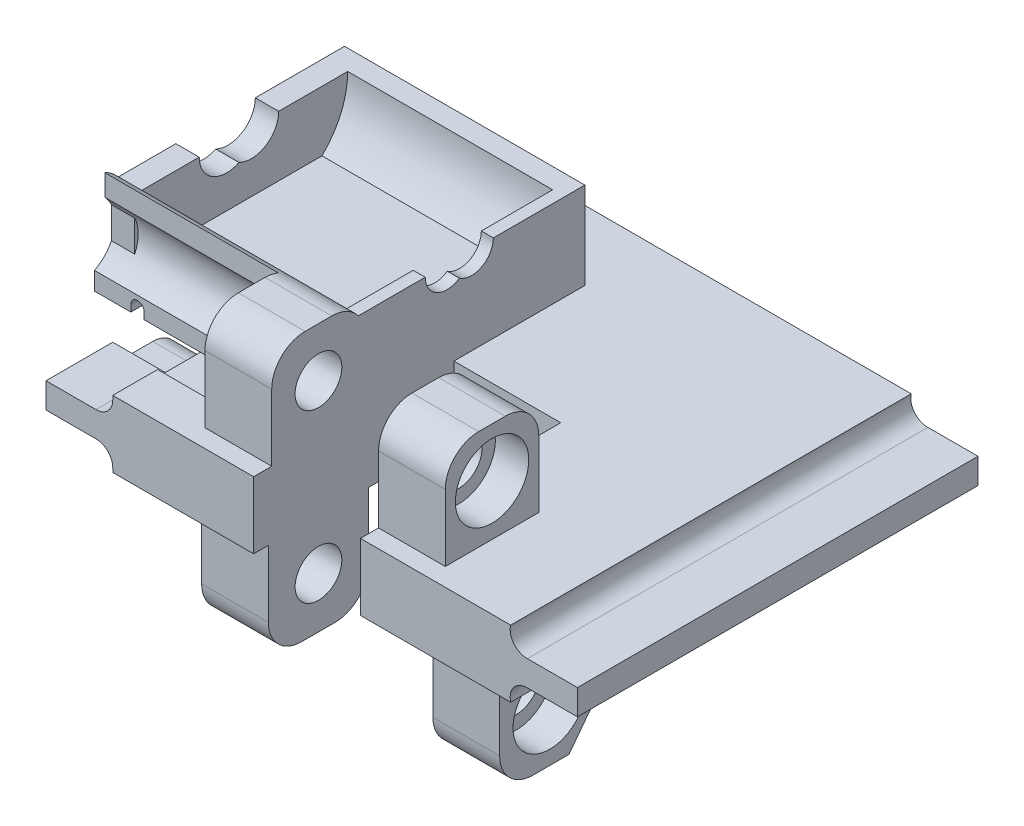
SolidWorks part; units mm, degrees
material "ABS"
ref_plane "정면" through (0, 0, 0) normal (0, 0, 1) x (1, 0, 0)
ref_plane "윗면" through (0, 0, 0) normal (0, 1, 0) x (1, 0, 0)
ref_plane "우측면" through (0, 0, 0) normal (1, 0, 0) x (0, 0, -1)
sketch "스케치1" plane through (0, 0, 0) normal (0, 0, 1) x (1, 0, 0)
  line L0 (0, 0) -> (0, 10)
  line L1 (29.8, 10) -> (-29.8, 10)
  line L2 (-32.3, 6.9) -> (-39.8, 6.9)
  line L3 (-39.8, 6.9) -> (-39.8, 3.1)
  line L4 (-39.8, 3.1) -> (-32.3, 3.1)
  line L5 (-29.8, 0) -> (29.8, 0)
  line L6 (39.8, 3.1) -> (32.3, 3.1)
  line L7 (39.8, 6.9) -> (39.8, 3.1)
  line L8 (32.3, 6.9) -> (39.8, 6.9)
  line L9 (-29.8, 10) -> (-29.8, 9.4)
  line L10 (-29.8, 0.6) -> (-29.8, 0)
  arc A2 (32.3, 3.1) -> (29.8, 0) centre (32.2267, 0.6011) ccw
  arc A3 (29.8, 10) -> (32.3, 6.9) centre (32.2267, 9.3989) ccw
  arc A5 (-32.3, 3.1) -> (-29.8, 0.6) centre (-32.3, 0.6) cw
  arc A6 (-29.8, 9.4) -> (-32.3, 6.9) centre (-32.3, 9.4) cw
  point P13 (0, 5)
  point P14 (-39.8, 5)
  dimension "D5" = 2.5
  dimension "D6" = 2.5
  dimension "D1" = 39.8
  dimension "D2" = 29.8
  dimension "D3" = 10
  dimension "D4" = 29.8
  dimension "D7" = 3.8
extrude "보스-돌출1" add sketch "스케치1" along normal blind 60
sketch "스케치2" plane through (-39.8, 0, 0) normal (-1, 0, 0) x (0, 0, 1)
  line L1 (44, 4) -> (50, 4)
  line L2 (50, 4) -> (50, 8)
  line L3 (16, 4) -> (10, 4)
  line L4 (50, 8) -> (10, 8)
  line L5 (30, 8) -> (30, 0)
  line L6 (20, 0) -> (40, 0)
  line L7 (60, 6.9) -> (60, 3.1) construction
  line L8 (10, 4) -> (10, 8)
  line L9 (60, 0) -> (0, 0) construction
  arc A0 (40, 0) -> (44, 4) centre (44, 0) cw
  arc A1 (20, 0) -> (16, 4) centre (16, 0) ccw
  line M12 (0, 3.1) -> (60, 3.1)
  line M14 (60, 6.9) -> (0, 6.9)
  dimension "D4" = 4
  dimension "D1" = 4
  dimension "D2" = 4
  dimension "D3" = 10
  dimension "D5" = 20
  dimension "D6" = 10
extrude "컷-돌출1" cut sketch "스케치2" against normal blind 17.3 contours A1 L5 L8 L3 M12 M14 | L6 A0 L5 M12 | A0 L1 L2 L5 M12 M14
sketch "Sketch1" plane through (0, 10, 0) normal (0, 1, 0) x (1, 0, 0)
  line L0 (29.8, -60) -> (-29.8, -60) construction
  line L1 (7.3, -60) -> (-8.7, -60)
  line L2 (7.3, -60) -> (7.3, -30)
  line L3 (7.3, -30) -> (-8.7, -30)
  line L4 (-8.7, -60) -> (-8.7, -30)
  line L5 (29.8, -60) -> (29.8, 0) construction
  dimension "D1" = 22.5
  dimension "D2" = 30
  dimension "D3" = 16
extrude "Cut-Extrude1" cut sketch "Sketch1" against normal blind 10
sketch "Sketch2" plane through (7.3, 0, 0) normal (-1, 0, 0) x (0, 0, 1)
  line L0 (60, 10) -> (30, 10) construction
  line L6 (57.29, 10) -> (43.29, 10)
  line L7 (57.29, 10) -> (57.29, 20)
  line L8 (52.29, 25) -> (48.29, 25)
  line L9 (43.29, 10) -> (43.29, 20)
  circle A0 centre (50.29, 17.61) radius 3.5
  arc A3 (48.29, 25) -> (43.29, 20) centre (48.29, 20) ccw
  arc A4 (57.29, 20) -> (52.29, 25) centre (52.29, 20) ccw
  point P1 (50.29, 25)
  point P11 (43.29, 25)
  point P15 (57.29, 25)
  dimension "D1" = 7
  dimension "D2" = 14
  dimension "D6" = 5
  dimension "D3" = 7.61
  dimension "D4" = 9.71
  dimension "D5" = 15
extrude "Boss-Extrude1" add sketch "Sketch2" against normal blind 10
sketch "Sketch4" plane through (17.3, 0, 0) normal (1, 0, 0) x (0, 0, -1)
  circle A0 centre (-50.29, 17.61) radius 5.5
  dimension "D1" = 11
extrude "Cut-Extrude4" cut sketch "Sketch4" against normal blind 5
ref_plane "Plane1" through (-0.7, 0, 0) normal (-1, 0, 0) x (0, 0, 1)
mirror "Mirror1" about plane through (-0.7, 0, 0) normal (-1, 0, 0) of "Cut-Extrude4", "Boss-Extrude1"
sketch "Sketch5" plane through (-8.7, 0, 0) normal (1, 0, 0) x (0, 0, -1)
  line L0 (-30, 0) -> (-60, 0) construction
  line L1 (-60, 0) -> (-60, 10) construction
  line L3 (-57.79, 0) -> (-42.79, 0)
  line L4 (-57.79, 0) -> (-57.79, -10)
  line L5 (-52.79, -15) -> (-47.79, -15)
  line L6 (-42.79, 0) -> (-42.79, -10)
  circle A0 centre (-50.29, -7.39) radius 3.5
  arc A1 (-47.79, -15) -> (-42.79, -10) centre (-47.79, -10) ccw
  arc A2 (-57.79, -10) -> (-52.79, -15) centre (-52.79, -10) ccw
  point P11 (-50.29, -15)
  point P14 (-42.79, -15)
  point P17 (-57.79, -15)
  dimension "D1" = 7
  dimension "D6" = 5
  dimension "D2" = 7.39
  dimension "D3" = 9.71
  dimension "D4" = 15
  dimension "D5" = 15
extrude "Boss-Extrude2" add sketch "Sketch5" against normal blind 10
sketch "Sketch6" plane through (-18.7, 0, 0) normal (-1, 0, 0) x (0, 0, 1)
  circle A0 centre (50.29, -7.39) radius 5.5
  dimension "D1" = 11
extrude "Cut-Extrude5" cut sketch "Sketch6" against normal blind 5
ref_plane "Plane2" through (3.62, 0, 0) normal (1, 0, 0) x (0, 0, -1)
mirror "Mirror2" about plane through (3.62, 0, 0) normal (1, 0, 0) of "Cut-Extrude5", "Boss-Extrude2"
sketch "Sketch7" plane through (-8.7, 0, 0) normal (1, 0, 0) x (0, 0, -1)
  line L0 (-30, 0) -> (-30, 10) construction
  line L1 (-30, 10) -> (-43.29, 10) construction
  line L2 (-40.0582, 14) -> (-17.2618, 14)
  line L4 (-39.4431, 32.6025) -> (-17.8769, 32.6025)
  line L8 (-46.1326, 23.0254) -> (-10.3854, 23.0254)
  line L9 (-46.1326, 36.0509) -> (-10.3854, 36.0509)
  line L10 (-46.1326, 36.0509) -> (-46.1326, 10)
  line L11 (-46.1326, 10) -> (-10.3854, 10)
  line L12 (-10.3854, 36.0509) -> (-10.3854, 10)
  arc A1 (-17.2618, 14) -> (-17.8769, 32.6025) centre (-25.91, 23.0254) ccw
  arc A2 (-39.4431, 32.6025) -> (-40.0582, 14) centre (-31.41, 23.0254) ccw
  dimension "D2" = 12.5
  dimension "D6" = 12.5
  dimension "D1" = 4.09
  dimension "D3" = 4
  dimension "D4" = 5.5
  dimension "D5" = 22.6025
extrude "Boss-Extrude4" add sketch "Sketch7" against normal blind 36
sketch "Sketch8" plane through (0, 23.0254, 0) normal (0, 1, 0) x (1, 0, 0)
  line L1 (-8.7, -13.41) -> (-10.5, -13.41)
  line L2 (-8.7, -13.41) -> (-8.7, -45.828)
  line L3 (-8.7, -45.828) -> (-10.5, -45.828)
  line L4 (-10.5, -13.41) -> (-10.5, -45.828)
  line L6 (-44.7, -13.41) -> (-41.2, -13.41)
  line L7 (-44.7, -13.41) -> (-44.7, -45.3107)
  line L8 (-44.7, -45.3107) -> (-41.2, -45.3107)
  line L9 (-41.2, -13.41) -> (-41.2, -45.3107)
  dimension "D1" = 1.8
  dimension "D2" = 3.5
extrude "Boss-Extrude5" add sketch "Sketch8" against normal blind 10
sketch "Sketch9" plane through (-8.7, 0, 0) normal (1, 0, 0) x (0, 0, -1)
  line L0 (-44.3092, 23.0254) -> (-10.3854, 23.0254) construction
  line L1 (-44.3092, 23.0254) -> (-10.3854, 23.0254) construction
  circle A0 centre (-27.3473, 23.0254) radius 3.25
  circle A1 centre (-31.0473, 23.0254) radius 3.25
  line M2 (-10.3854, 23.0254) -> (-44.3092, 23.0254)
  dimension "D1" = 6.5
  dimension "D2" = 6.5
  dimension "D3" = 3.7
extrude "Cut-Extrude6" cut sketch "Sketch9" against normal blind 10 contours A1 A0 M2 | A1 A0 M2
sketch "Sketch10" plane through (-44.7, 0, 0) normal (-1, 0, 0) x (0, 0, 1)
  line L0 (45.3107, 23.0254) -> (10.3854, 23.0254) construction
  line L1 (45.3107, 23.0254) -> (10.3854, 23.0254) construction
  circle A0 centre (27.8481, 23.0254) radius 4.1
  circle A1 centre (31.5481, 23.0254) radius 4.1
  line M10 (45.3107, 23.0254) -> (10.3854, 23.0254)
  dimension "D1" = 8.2
  dimension "D2" = 8.2
  dimension "D3" = 3.7
extrude "Cut-Extrude7" cut sketch "Sketch10" against normal blind 10 contours A1 A0 M10 | A1 A0 M10 | A0 A1 M10
sketch "Sketch12" plane through (25.94, 0, 0) normal (1, 0, 0) x (0, 0, -1)
  line L0 (-42.79, -8.9362) -> (-47.4024, -14.985)
  line L1 (-42.79, -10) -> (-42.79, 0) construction
  line L2 (-47.4024, -14.985) -> (-43.1675, -15.5436)
  line L3 (-43.1675, -15.5436) -> (-40.8892, -10)
  line L4 (-40.8892, -10) -> (-42.79, -8.9362)
  arc A0 (-47.79, -15) -> (-42.79, -10) centre (-47.79, -10) ccw construction
extrude "Cut-Extrude9" cut sketch "Sketch12" against normal blind 10
sketch "Sketch13" plane through (0, 0, 43.29) normal (0, 0, 1) x (1, 0, 0)
  line L0 (-29.8, 10) -> (-23.7804, 10)
  line L1 (-29.8, 10) -> (-18.7, 10) construction
  line L2 (-23.7804, 10) -> (-23.7804, 11.1029)
  line L3 (-21.7804, 11.1029) -> (-21.7804, 9)
  line L4 (-21.7804, 9) -> (-30.476, 9)
  line L5 (-30.476, 9) -> (-29.8, 10)
  arc A0 (-23.7804, 11.1029) -> (-21.7804, 11.1029) centre (-22.7804, 11.1029) cw
  dimension "D2" = 1
  dimension "D1" = 1
extrude "Cut-Extrude10" cut sketch "Sketch13" against normal blind 35 and the other way blind 10
sketch "Sketch11" plane through (0, 0, 43.29) normal (0, 0, 1) x (1, 0, 0)
  line L0 (-39.25, 10) -> (-39.25, 11)
  line L2 (-37.25, 11) -> (-37.25, 10)
  line L3 (-37.25, 10) -> (-39.25, 10)
  arc A0 (-39.25, 11) -> (-37.25, 11) centre (-38.25, 11) cw
  dimension "D1" = 1
  dimension "D2" = 1
  dimension "D3" = 2
extrude "Cut-Extrude8" cut sketch "Sketch11" against normal through all and the other way blind 24
sketch "Sketch14" plane through (-18.7, 0, 0) normal (-1, 0, 0) x (0, 0, 1)
  line L1 (47.8417, 12.685) -> (47.8417, 10)
  line L2 (43.29, 10) -> (57.29, 10) construction
  line L3 (47.8417, 10) -> (43.29, 10)
  line L4 (43.29, 10) -> (43.29, 20)
  circle A0 centre (50.29, 17.61) radius 5.5 construction
  arc A1 (46.2859, 21.3806) -> (47.8417, 12.685) centre (50.29, 17.61) ccw
sketch "Sketch17" plane through (-18.7, 0, 0) normal (-1, 0, 0) x (0, 0, 1)
  line L0 (43.29, 10) -> (47.8417, 10)
  line L1 (47.8417, 10) -> (47.8417, 12.685)
  line L2 (46.2859, 21.3806) -> (46.2859, 24.5808)
  line L3 (43.29, 20) -> (43.29, 10)
  arc A0 (47.8417, 12.685) -> (46.2859, 21.3806) centre (50.29, 17.61) cw
  arc A1 (48.29, 25) -> (43.29, 20) centre (48.29, 20) ccw construction
  arc A2 (46.2859, 24.5808) -> (43.29, 20) centre (48.29, 20) ccw
  arc A3 (46.2859, 21.3806) -> (47.8417, 12.685) centre (50.29, 17.61) ccw construction
extrude "Boss-Extrude8" add sketch "Sketch17" along normal up to surface (26 mm away) up to face at (-44.7, 17.1326, 31.8963)
sketch "Sketch16" plane through (-10.5, 0, 0) normal (-1, 0, 0) x (0, 0, 1)
  line L0 (39.21, 14) -> (40.0582, 14)
  line L1 (40.0582, 14) -> (17.2618, 14) construction
  line L2 (34.2973, 23.0254) -> (44.3092, 23.0254) construction
  line L3 (43.91, 23.0254) -> (41.1378, 23.0254)
  line L4 (41.1378, 23.0254) -> (39.21, 14)
  arc A0 (40.0582, 14) -> (43.91, 23.0254) centre (31.41, 23.0254) ccw
  arc A1 (40.0582, 14) -> (43.29, 19.1376) centre (31.41, 23.0254) ccw construction
extrude "Cut-Extrude12" cut sketch "Sketch16" along normal up to surface (30.7 mm away) up to face at (-41.2, 19.4189, 32.2066)
sketch "Sketch18" plane through (0, 0, 43.29) normal (0, 0, -1) x (-1, 0, 0)
  line L6 (21.7804, 11.1029) -> (21.7804, 10)
  line L7 (21.7804, 10) -> (23.7804, 10)
  line L8 (23.7804, 10) -> (23.7804, 11.1029)
  line L9 (21.7804, 11.1029) -> (21.7804, 10)
  line L10 (21.7804, 10) -> (23.7804, 10)
  line L11 (23.7804, 10) -> (23.7804, 11.1029)
  arc A2 (23.7804, 11.1029) -> (21.7804, 11.1029) centre (22.7804, 11.1029) ccw
  arc A3 (23.7804, 11.1029) -> (21.7804, 11.1029) centre (22.7804, 11.1029) ccw
  dimension "D1" = 0
extrude "Cut-Extrude13" cut sketch "Sketch18" against normal up to surface (4.5517 mm away) up to face at (-29.7161, 11.074, 47.8417)
sketch "Sketch19" plane through (0, 0, 43.29) normal (0, 0, -1) x (-1, 0, 0)
  line L6 (37.25, 11) -> (37.25, 10)
  line L7 (37.25, 10) -> (39.25, 10)
  line L8 (39.25, 10) -> (39.25, 11)
  line L9 (37.25, 11) -> (37.25, 10)
  line L10 (37.25, 10) -> (39.25, 10)
  line L11 (39.25, 10) -> (39.25, 11)
  arc A2 (39.25, 11) -> (37.25, 11) centre (38.25, 11) ccw
  arc A3 (39.25, 11) -> (37.25, 11) centre (38.25, 11) ccw
  dimension "D1" = 0
extrude "Cut-Extrude14" cut sketch "Sketch19" against normal blind 14
